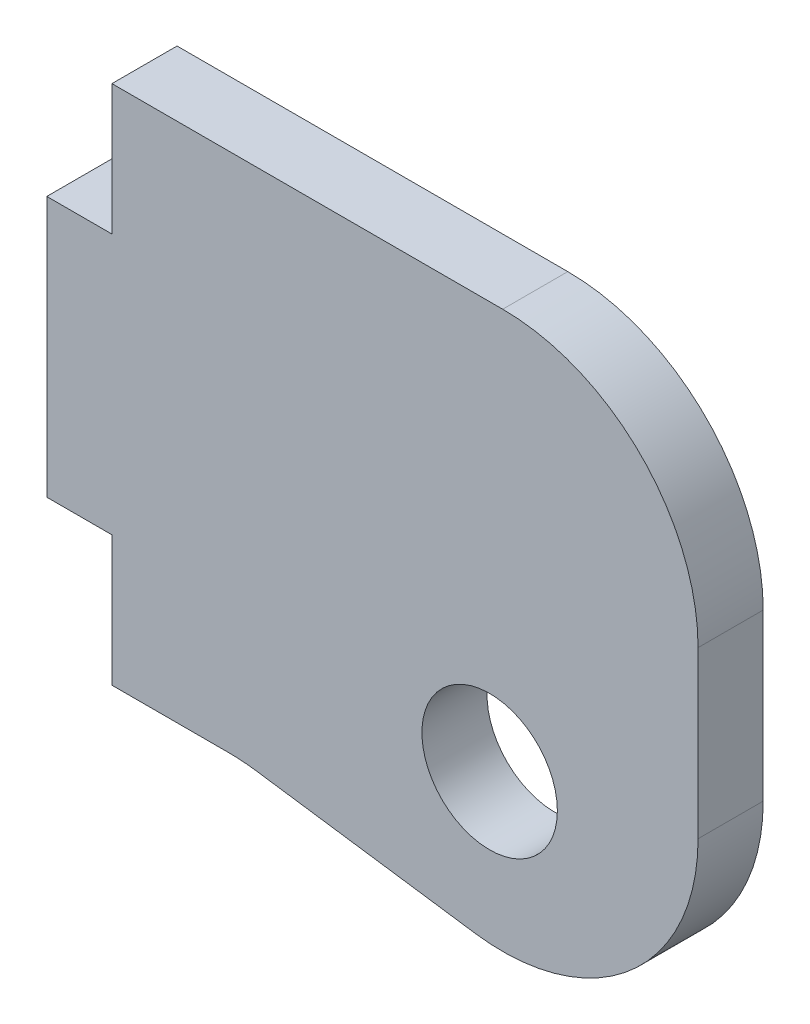
SolidWorks part; units mm, degrees
material "AISI 4340 Steel, normalized"
ref_plane "X-Y Datum" through (0, 0, 0) normal (0, 0, 1) x (1, 0, 0)
ref_plane "X-Z Datum" through (0, 0, 0) normal (0, 1, 0) x (1, 0, 0)
ref_plane "Y-Z Datum" through (0, 0, 0) normal (1, 0, 0) x (0, 0, -1)
sketch "Sketch1" plane through (0, 0, 0) normal (0, 0, 1) x (1, 0, 0)
  line L0 (0, 12.7) -> (0, -12.7)
  line L7 (31.75, -15.875) -> (31.75, 12.7)
  line L8 (31.75, 12.7) -> (0, 12.7)
  line L9 (0, -12.7) -> (9.525, -12.7)
  line L10 (9.525, -12.7) -> (31.75, -15.875)
  point P2 (0, 0)
  dimension "D1" = 25.4
  dimension "D2" = 31.75
  dimension "D3" = 28.575
  dimension "D4" = 9.525
extrude "Boss-Extrude1" add sketch "Sketch1" along normal blind 3.175
sketch "Sketch2" plane through (0, 0, 3.175) normal (0, 0, 1) x (1, 0, 0)
  circle A0 centre (21.5883, -7.1409) radius 3.302
  dimension "D1" = 6.604
extrude "Cut-Extrude1" cut sketch "Sketch2" against normal blind 3.175
fillet "Fillet1" radius 9.525 3 edges at (31.75, 12.7, 1.5875) (9.525, -12.7, 1.5875) (31.75, -15.875, 1.5875)
sketch "Sketch3" plane through (0, 0, 3.175) normal (0, 0, 1) x (1, 0, 0)
  line L1 (0, -12.7) -> (3.175, -12.7)
  line L2 (0, -12.7) -> (0, -6.35)
  line L3 (0, -6.35) -> (3.175, -6.35)
  line L4 (3.175, -12.7) -> (3.175, -6.35)
  line L5 (0, 12.7) -> (3.175, 12.7)
  line L6 (0, 12.7) -> (0, 6.35)
  line L7 (0, 6.35) -> (3.175, 6.35)
  line L8 (3.175, 12.7) -> (3.175, 6.35)
  dimension "D1" = 3.175
  dimension "D2" = 12.7
extrude "Cut-Extrude2" cut sketch "Sketch3" against normal blind 3.175
